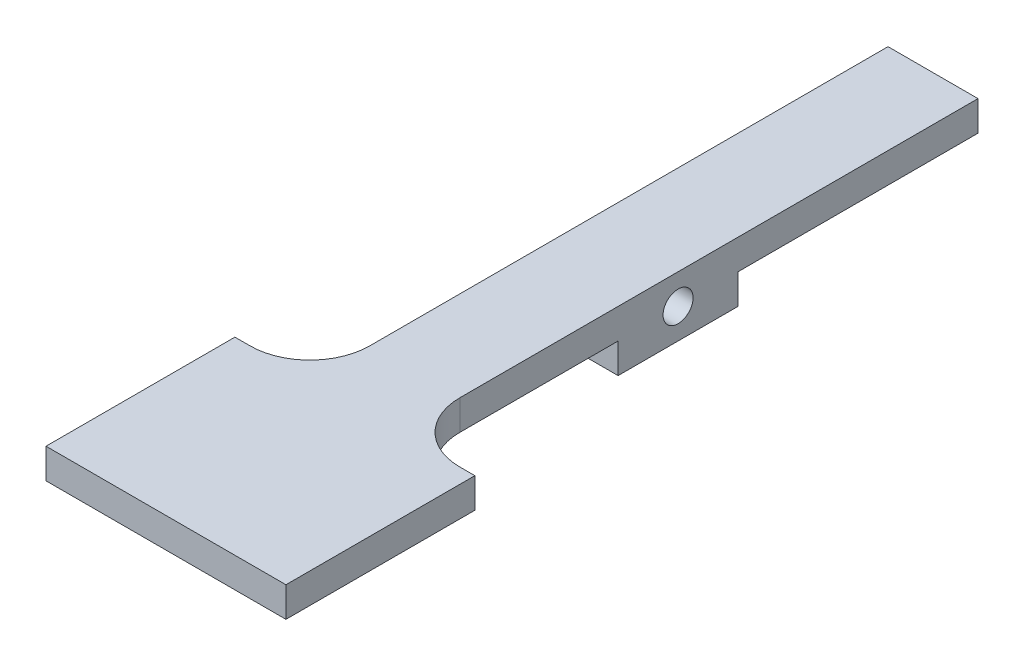
SolidWorks part; units mm, degrees
material "6061 Alloy"
ref_plane "Front Plane" through (0, 0, 0) normal (0, 0, 1) x (1, 0, 0)
ref_plane "Top Plane" through (0, 0, 0) normal (0, 1, 0) x (1, 0, 0)
ref_plane "Right Plane" through (0, 0, 0) normal (1, 0, 0) x (0, 0, -1)
sketch "Sketch1" plane through (0, 0, 0) normal (1, 0, 0) x (0, 0, -1)
  line L0 (0, 1.5875) -> (0, -1.5875)
  line L1 (0, -1.5875) -> (-25.4, -1.5875)
  line L5 (-76.2, 1.5875) -> (0, 1.5875)
  line L6 (-38.1, -1.5875) -> (-76.2, -1.5875)
  line L8 (-38.1, -1.5875) -> (-38.1, -4.7625)
  line L9 (-38.1, -4.7625) -> (-25.4, -4.7625)
  line L10 (-25.4, -1.5875) -> (-25.4, -4.7625)
  line L11 (-76.2, 1.5875) -> (-76.2, -1.5875)
  circle A0 centre (-31.75, -1.5875) radius 1.5875
  point P14 (-31.75, -4.7625)
  dimension "D6" = 3.175
  dimension "D1" = 3.175
  dimension "D4" = 76.2
  dimension "D5" = 3.175
  dimension "D7" = 12.7
  dimension "D8" = 38.1
extrude "Boss-Extrude1" add sketch "Sketch1" along normal blind 9.525
ref_plane "Center Plane" through (4.7625, 0, 0) normal (1, 0, 0) x (0, 0, -1)
sketch "Sketch3" plane through (4.7625, 0, 0) normal (1, 0, 0) x (0, 0, -1)
  line L2 (-76.2, -1.5875) -> (-61.2, -1.5875)
  line L4 (-61.2, -1.5875) -> (-61.2, 1.5875)
  line L5 (-76.2, 1.5875) -> (0, 1.5875) construction
  line L6 (-61.2, 1.5875) -> (-76.2, 1.5875)
  line L7 (-76.2, 1.5875) -> (-76.2, -1.5875)
  line L9 (-76.2, 1.5875) -> (-81.2, 1.5875)
  line L10 (-76.2, 1.5875) -> (-76.2, -1.5875)
  line L11 (-76.2, -1.5875) -> (-81.2, -1.5875)
  line L12 (-81.2, 1.5875) -> (-81.2, -1.5875)
  line L13 (-76.2, 1.5875) -> (-76.2, -1.5875) construction
  line L14 (-38.1, -1.5875) -> (-76.2, -1.5875) construction
  dimension "D1" = 15
  dimension "D2" = 20
extrude "Boss-Extrude2" add sketch "Sketch3" along normal mid plane 25.4 contours L6 L7 L2 L4 | L9 L12 L11 L7
fillet "Fillet1" radius 6.35 2 edges at (0, 0, 61.2) (9.525, 0, 61.2)
